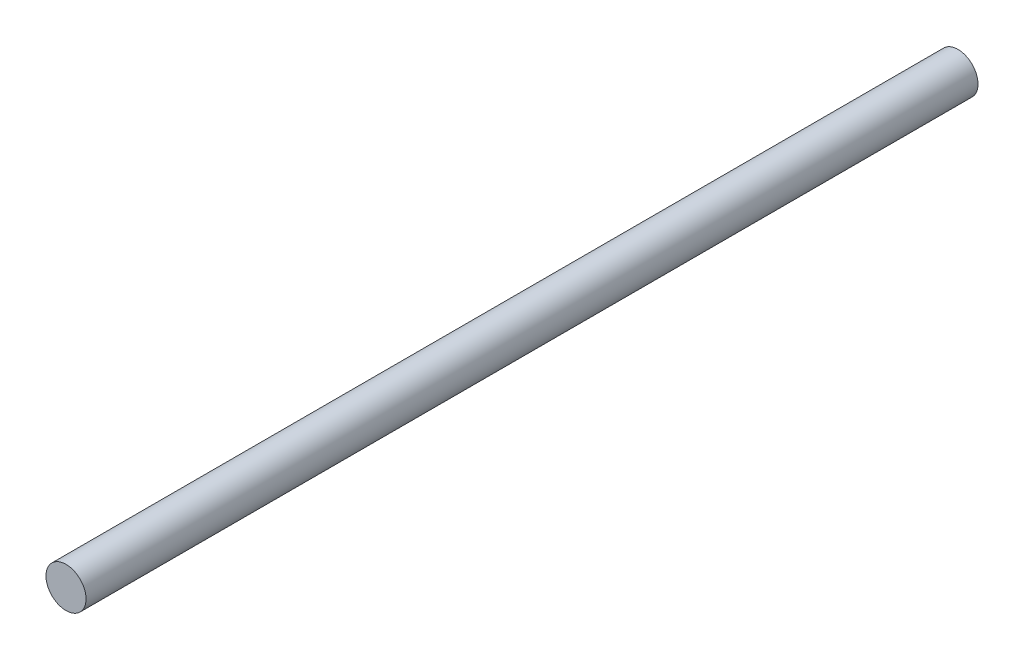
SolidWorks part; units mm, degrees
ref_plane "Front Plane" through (0, 0, 0) normal (0, 0, 1) x (1, 0, 0)
ref_plane "Top Plane" through (0, 0, 0) normal (0, 1, 0) x (1, 0, 0)
ref_plane "Right Plane" through (0, 0, 0) normal (1, 0, 0) x (0, 0, -1)
sketch "Sketch1" plane through (0, 0, 0) normal (0, 0, 1) x (1, 0, 0)
  circle A0 centre (0, 0) radius 4
extrude "Boss-Extrude1" add sketch "Sketch1" along normal mid plane 178
